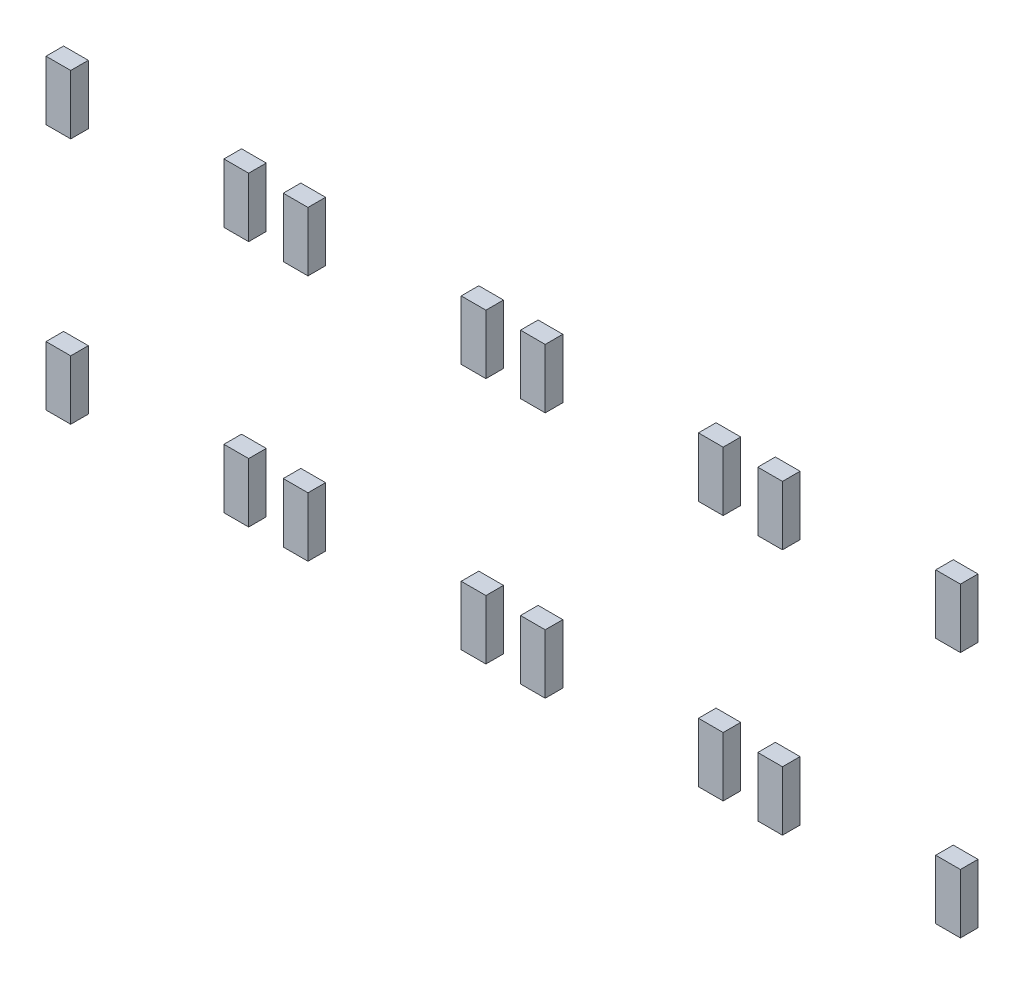
SolidWorks part; units mm, degrees
ref_plane "Front Plane" through (0, 0, 0) normal (0, 0, 1) x (1, 0, 0)
ref_plane "Top Plane" through (0, 0, 0) normal (0, 1, 0) x (1, 0, 0)
ref_plane "Right Plane" through (0, 0, 0) normal (1, 0, 0) x (0, 0, -1)
sketch "Sketch1" plane through (0, 0, 0) normal (0, 0, 1) x (1, 0, 0)
  line L0 (24.25, -34.5) -> (21.75, -34.5)
  line L1 (6.25, -34.5) -> (3.75, -34.5)
  line L2 (6.25, -34.5) -> (6.25, -40.5)
  line L3 (6.25, -40.5) -> (3.75, -40.5)
  line L4 (3.75, -34.5) -> (3.75, -40.5)
  line L5 (24.25, -34.5) -> (24.25, -40.5)
  line L6 (24.25, -40.5) -> (21.75, -40.5)
  line L7 (21.75, -34.5) -> (21.75, -40.5)
  line L8 (6.25, -59.5) -> (3.75, -59.5)
  line L9 (6.25, -59.5) -> (6.25, -65.5)
  line L10 (6.25, -65.5) -> (3.75, -65.5)
  line L11 (3.75, -59.5) -> (3.75, -65.5)
  line L12 (24.25, -59.5) -> (21.75, -59.5)
  line L13 (24.25, -59.5) -> (24.25, -65.5)
  line L14 (24.25, -65.5) -> (21.75, -65.5)
  line L15 (21.75, -59.5) -> (21.75, -65.5)
  line L16 (48.25, -34.5) -> (45.75, -34.5)
  line L17 (30.25, -34.5) -> (27.75, -34.5)
  line L18 (30.25, -34.5) -> (30.25, -40.5)
  line L19 (30.25, -40.5) -> (27.75, -40.5)
  line L20 (27.75, -34.5) -> (27.75, -40.5)
  line L21 (48.25, -34.5) -> (48.25, -40.5)
  line L22 (48.25, -40.5) -> (45.75, -40.5)
  line L23 (45.75, -34.5) -> (45.75, -40.5)
  line L24 (30.25, -59.5) -> (27.75, -59.5)
  line L25 (30.25, -59.5) -> (30.25, -65.5)
  line L26 (30.25, -65.5) -> (27.75, -65.5)
  line L27 (27.75, -59.5) -> (27.75, -65.5)
  line L28 (48.25, -59.5) -> (45.75, -59.5)
  line L29 (48.25, -59.5) -> (48.25, -65.5)
  line L30 (48.25, -65.5) -> (45.75, -65.5)
  line L31 (45.75, -59.5) -> (45.75, -65.5)
  line L32 (72.25, -34.5) -> (69.75, -34.5)
  line L33 (54.25, -34.5) -> (51.75, -34.5)
  line L34 (54.25, -34.5) -> (54.25, -40.5)
  line L35 (54.25, -40.5) -> (51.75, -40.5)
  line L36 (51.75, -34.5) -> (51.75, -40.5)
  line L37 (72.25, -34.5) -> (72.25, -40.5)
  line L38 (72.25, -40.5) -> (69.75, -40.5)
  line L39 (69.75, -34.5) -> (69.75, -40.5)
  line L40 (54.25, -59.5) -> (51.75, -59.5)
  line L41 (54.25, -59.5) -> (54.25, -65.5)
  line L42 (54.25, -65.5) -> (51.75, -65.5)
  line L43 (51.75, -59.5) -> (51.75, -65.5)
  line L44 (72.25, -59.5) -> (69.75, -59.5)
  line L45 (72.25, -59.5) -> (72.25, -65.5)
  line L46 (72.25, -65.5) -> (69.75, -65.5)
  line L47 (69.75, -59.5) -> (69.75, -65.5)
  line L48 (96.25, -34.5) -> (93.75, -34.5)
  line L49 (78.25, -34.5) -> (75.75, -34.5)
  line L50 (78.25, -34.5) -> (78.25, -40.5)
  line L51 (78.25, -40.5) -> (75.75, -40.5)
  line L52 (75.75, -34.5) -> (75.75, -40.5)
  line L53 (96.25, -34.5) -> (96.25, -40.5)
  line L54 (96.25, -40.5) -> (93.75, -40.5)
  line L55 (93.75, -34.5) -> (93.75, -40.5)
  line L56 (78.25, -59.5) -> (75.75, -59.5)
  line L57 (78.25, -59.5) -> (78.25, -65.5)
  line L58 (78.25, -65.5) -> (75.75, -65.5)
  line L59 (75.75, -59.5) -> (75.75, -65.5)
  line L60 (96.25, -59.5) -> (93.75, -59.5)
  line L61 (96.25, -59.5) -> (96.25, -65.5)
  line L62 (96.25, -65.5) -> (93.75, -65.5)
  line L63 (93.75, -59.5) -> (93.75, -65.5)
  dimension "D1" = 4
extrude "Boss-Extrude1" add sketch "Sketch1" along normal blind 1.78
